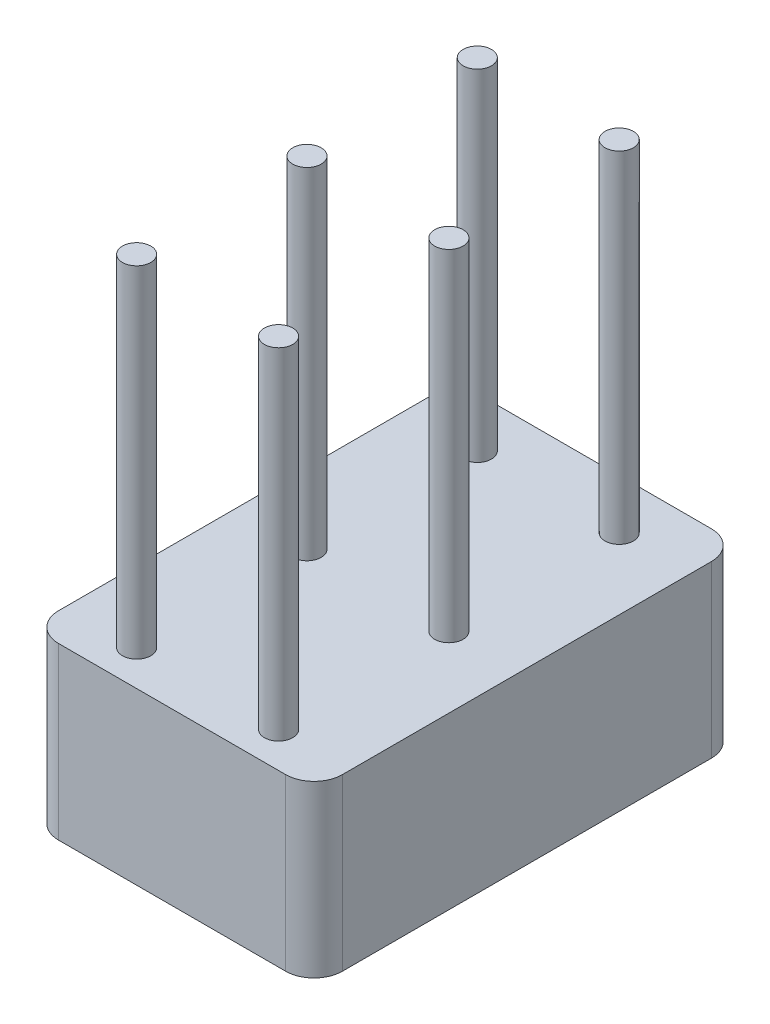
SolidWorks part; units mm, degrees
material "ABS"
ref_plane "Front Plane" through (0, 0, 0) normal (0, 0, 1) x (1, 0, 0)
ref_plane "Top Plane" through (0, 0, 0) normal (0, 1, 0) x (1, 0, 0)
ref_plane "Right Plane" through (0, 0, 0) normal (1, 0, 0) x (0, 0, -1)
sketch "Sketch1" plane through (0, 0, 0) normal (0, 1, 0) x (1, 0, 0)
  line L1 (-2, 3.75) -> (2, 3.75)
  line L2 (-2.5, 3.25) -> (-2.5, -3.25)
  line L3 (-2, -3.75) -> (2, -3.75)
  line L4 (2.5, 3.25) -> (2.5, -3.25)
  line L5 (-2.5, 3.75) -> (2.5, -3.75) construction
  line L6 (-2.5, -3.75) -> (2.5, 3.75) construction
  arc A0 (2.5, 3.25) -> (2, 3.75) centre (2, 3.25) ccw
  arc A1 (2.5, -3.25) -> (2, -3.75) centre (2, -3.25) cw
  arc A2 (-2, -3.75) -> (-2.5, -3.25) centre (-2, -3.25) cw
  arc A3 (-2, 3.75) -> (-2.5, 3.25) centre (-2, 3.25) ccw
  point P0 (0, 0)
  dimension "D3" = 0.5
  dimension "D4" = 0.5
  dimension "D1" = 5
  dimension "D2" = 7.5
extrude "Boss-Extrude1" add sketch "Sketch1" along normal blind 3
sketch "Sketch2" plane through (0, 3, 0) normal (0, 1, 0) x (1, 0, 0)
  line L0 (0, 3.75) -> (0, -3.75) construction
  line L1 (2, 3.75) -> (-2, 3.75) construction
  line L2 (-2, -3.75) -> (2, -3.75) construction
  line L3 (0, 3.75) -> (-2.5, 3.75) construction
  circle A0 centre (-1.25, 2.8754) radius 0.25
  circle A1 centre (1.25, 2.8754) radius 0.25
  circle A2 centre (-1.25, -0.1246) radius 0.25
  circle A3 centre (1.25, -0.1246) radius 0.25
  circle A4 centre (-1.25, -3.1246) radius 0.25
  circle A5 centre (1.25, -3.1246) radius 0.25
  dimension "D1" = 0.5
  dimension "D2" = 3
extrude "Boss-Extrude2" add sketch "Sketch2" along normal blind 6
